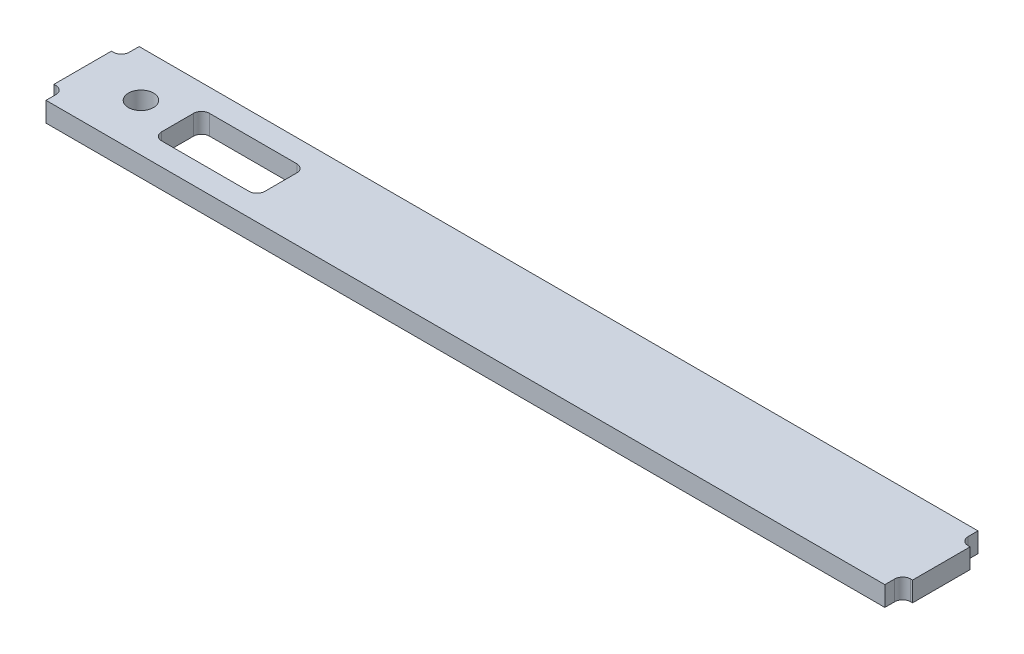
SolidWorks part; units mm, degrees
ref_plane "Front Plane" through (0, 0, 0) normal (0, 0, 1) x (1, 0, 0)
ref_plane "Top Plane" through (0, 0, 0) normal (0, 1, 0) x (1, 0, 0)
ref_plane "Right Plane" through (0, 0, 0) normal (1, 0, 0) x (0, 0, -1)
sketch "Sketch1" plane through (0, 0, 0) normal (0, 1, 0) x (1, 0, 0)
  line L1 (336.55, 37.3714) -> (-336.55, 37.3714)
  line L2 (336.55, 37.3714) -> (336.55, -37.3714)
  line L3 (336.55, -37.3714) -> (-336.55, -37.3714)
  line L4 (-336.55, 37.3714) -> (-336.55, -37.3714)
  line L5 (336.55, 37.3714) -> (-336.55, -37.3714) construction
  line L6 (336.55, -37.3714) -> (-336.55, 37.3714) construction
  point P0 (0, 0)
  dimension "D1" = 673.1
  dimension "D2" = 74.7428
extrude "Boss-Extrude1" add sketch "Sketch1" along normal blind 15.875
sketch "Sketch2" plane through (0, 15.875, 0) normal (0, 1, 0) x (1, 0, 0)
  line L0 (336.55, 37.3714) -> (-336.55, 37.3714) construction
  line L1 (344.4875, 18.3214) -> (-344.4875, 18.3214)
  line L2 (344.4875, 18.3214) -> (344.4875, -18.3214)
  line L3 (344.4875, -18.3214) -> (-344.4875, -18.3214)
  line L4 (-344.4875, 18.3214) -> (-344.4875, -18.3214)
  line L5 (344.4875, 18.3214) -> (-344.4875, -18.3214) construction
  line L6 (344.4875, -18.3214) -> (-344.4875, 18.3214) construction
  line L7 (-336.55, 37.3714) -> (-336.55, -37.3714) construction
  point P0 (0, 0)
  dimension "D1" = 19.05
  dimension "D2" = 7.9375
extrude "Boss-Extrude2" [suppressed] add sketch "Sketch2" against normal up to surface (15.875 mm away)
fillet "Fillet1" [suppressed] radius 6.35
sketch "Sketch3" plane through (0, 15.875, 0) normal (0, 1, 0) x (1, 0, 0)
  line L0 (-336.55, -37.3714) -> (336.55, -37.3714) construction
  line L2 (-336.55, 37.3714) -> (-336.55, -37.3714) construction
  circle A0 centre (-298.45, 0.7286) radius 10.1
  dimension "D3" = 20.2
  dimension "D1" = 38.1
  dimension "D2" = 38.1
extrude "Cut-Extrude1" cut sketch "Sketch3" against normal through all both and the other way through all
sketch "Sketch4" plane through (0, 15.875, 0) normal (0, 1, 0) x (1, 0, 0)
  line L0 (-336.55, 37.3714) -> (-336.55, -37.3714) construction
  line L1 (-336.55, 23.0839) -> (-344.4875, 23.0839)
  line L2 (-336.55, 23.0839) -> (-336.55, -23.0839)
  line L3 (-336.55, -23.0839) -> (-344.4875, -23.0839)
  line L4 (-344.4875, 23.0839) -> (-344.4875, -23.0839)
  line L5 (336.55, 37.3714) -> (-336.55, 37.3714) construction
  line L6 (-336.55, -37.3714) -> (336.55, -37.3714) construction
  line L7 (0, -5.1837) -> (0, 37.3714) construction
  line L8 (344.4875, 23.0839) -> (344.4875, -23.0839)
  line L9 (336.55, -23.0839) -> (344.4875, -23.0839)
  line L10 (336.55, 23.0839) -> (336.55, -23.0839)
  line L11 (336.55, 23.0839) -> (344.4875, 23.0839)
  dimension "D1" = 14.2875
  dimension "D2" = 14.2875
  dimension "D3" = 7.9375
  dimension "D4" = 688.975
extrude "Boss-Extrude3" add sketch "Sketch4" against normal up to surface (15.875 mm away) up to face at (-298.45, 0, 9.3714)
fillet "Fillet2" radius 6.35 4 edges at (336.55, 7.9375, 23.0839) (336.55, 7.9375, -23.0839) (-336.55, 7.9375, 23.0839) (-336.55, 7.9375, -23.0839)
sketch "Sketch5" plane through (0, 15.875, 0) normal (0, 1, 0) x (1, 0, 0)
  line L0 (0, 0) -> (-185.4835, 0) construction
  line L1 (-268.2875, -19.177) -> (-185.4835, -19.177)
  line L2 (-268.2875, -19.177) -> (-268.2875, 19.177)
  line L3 (-268.2875, 19.177) -> (-185.4835, 19.177)
  line L4 (-185.4835, -19.177) -> (-185.4835, 19.177)
  line L5 (-344.4875, 23.0839) -> (-344.4875, -23.0839) construction
  dimension "D1" = 82.804
  dimension "D2" = 38.354
  dimension "D3" = 76.2
extrude "Cut-Extrude2" cut sketch "Sketch5" against normal through all both and the other way through all
fillet "Fillet3" radius 6.35 4 edges at (-268.2875, 7.9375, -19.177) (-185.4835, 7.9375, -19.177) (-185.4835, 7.9375, 19.177) (-268.2875, 7.9375, 19.177)
